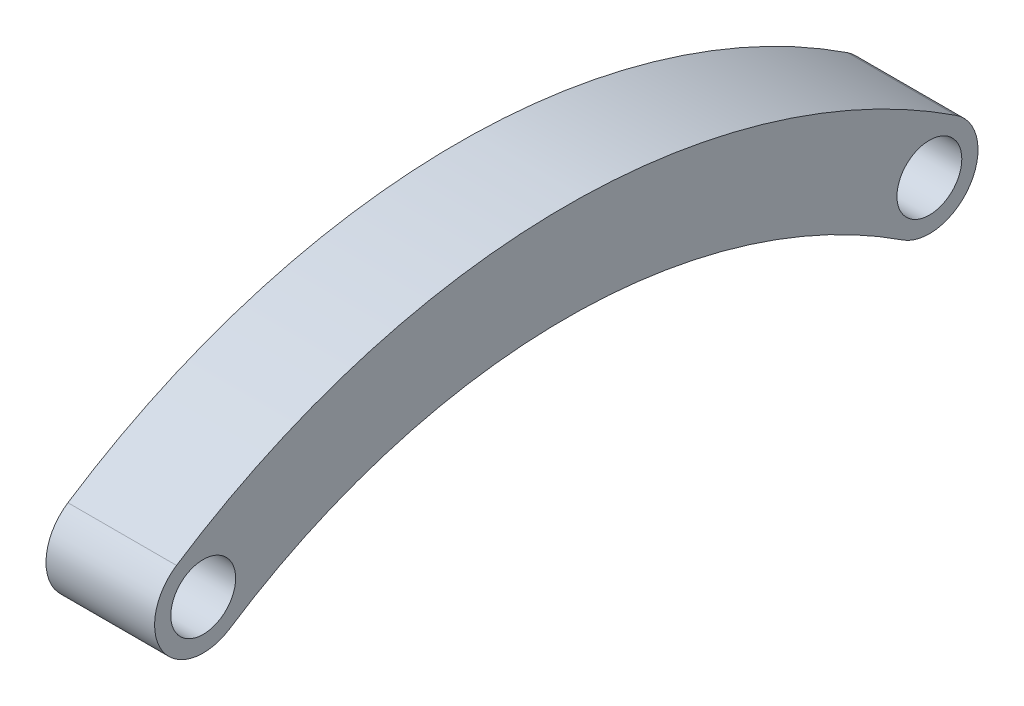
SolidWorks part; units mm, degrees
ref_plane "Front Plane" through (0, 0, 0) normal (0, 0, 1) x (1, 0, 0)
ref_plane "Top Plane" through (0, 0, 0) normal (0, 1, 0) x (1, 0, 0)
ref_plane "Right Plane" through (0, 0, 0) normal (1, 0, 0) x (0, 0, -1)
sketch "Sketch1" plane through (0, 0, 0) normal (1, 0, 0) x (0, 0, -1)
  line L0 (0, 55) -> (0, -55) construction
  line L1 (0, 0) -> (0, 6) construction
  line L2 (-22.4, -6.7) -> (22.4, -6.7) construction
  line L3 (81.1274, 6) -> (-72.2732, 6) construction
  line L4 (-25.4, 29.1562) -> (-25.4, -3.7) construction
  line L5 (25.4, 30.6853) -> (25.4, -3.7) construction
  arc A0 (0, 0) -> (20.7527, -6.2073) centre (0, -37.7948) cw
  arc A1 (0, 6) -> (24.0473, -1.1927) centre (0, -37.7948) cw
  arc A2 (20.7527, -6.2073) -> (24.0473, -1.1927) centre (22.4, -3.7) ccw
  arc A3 (-20.7527, -6.2073) -> (-24.0473, -1.1927) centre (-22.4, -3.7) cw
  arc A4 (0, 6) -> (-24.0473, -1.1927) centre (0, -37.7948) ccw
  arc A5 (0, 0) -> (-20.7527, -6.2073) centre (0, -37.7948) ccw
  circle A6 centre (22.4, -3.7) radius 2 construction
  dimension "D4" = 4
  dimension "D2" = 12.7
  dimension "D3" = 50.8
  dimension "D1" = 6
extrude "Boss-Extrude1" add sketch "Sketch1" along normal mid plane 6.7
sketch "Sketch2" plane through (3.35, 0, 0) normal (1, 0, 0) x (0, 0, -1)
  line L0 (0, 55) -> (0, -55) construction
  circle A0 centre (-22.4, -3.7) radius 2
  arc A1 (-24.0473, -1.1927) -> (-20.7527, -6.2073) centre (-22.4, -3.7) ccw construction
  circle A2 centre (22.4, -3.7) radius 2
  dimension "D1" = 4
extrude "Cut-Extrude1" cut sketch "Sketch2" against normal up to surface (6.7 mm away) up to face at (-3.35, -1.1736, 0)
